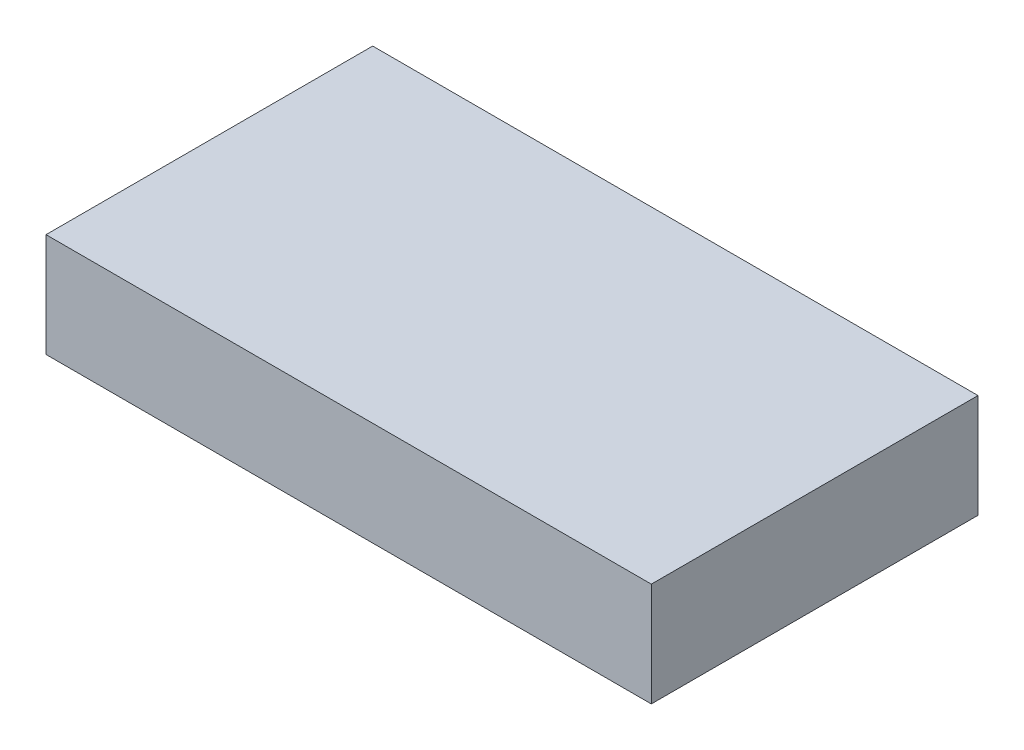
SolidWorks part; units mm, degrees
ref_plane "Front Plane" through (0, 0, 0) normal (0, 0, 1) x (1, 0, 0)
ref_plane "Top Plane" through (0, 0, 0) normal (0, 1, 0) x (1, 0, 0)
ref_plane "Right Plane" through (0, 0, 0) normal (1, 0, 0) x (0, 0, -1)
sketch "SPH Sketch" plane through (0, 0, 0) normal (0, 1, 0) x (1, 0, 0)
  line L1 (0, 0) -> (15.75, 0)
  line L2 (0, 0) -> (0, 8.5)
  line L3 (0, 8.5) -> (15.75, 8.5)
  line L4 (15.75, 0) -> (15.75, 8.5)
  dimension "SPHWidth" = 15.75
  dimension "SPH Length" = 8.5
extrude "SPH Extrude" add sketch "SPH Sketch" along normal blind 2.7
